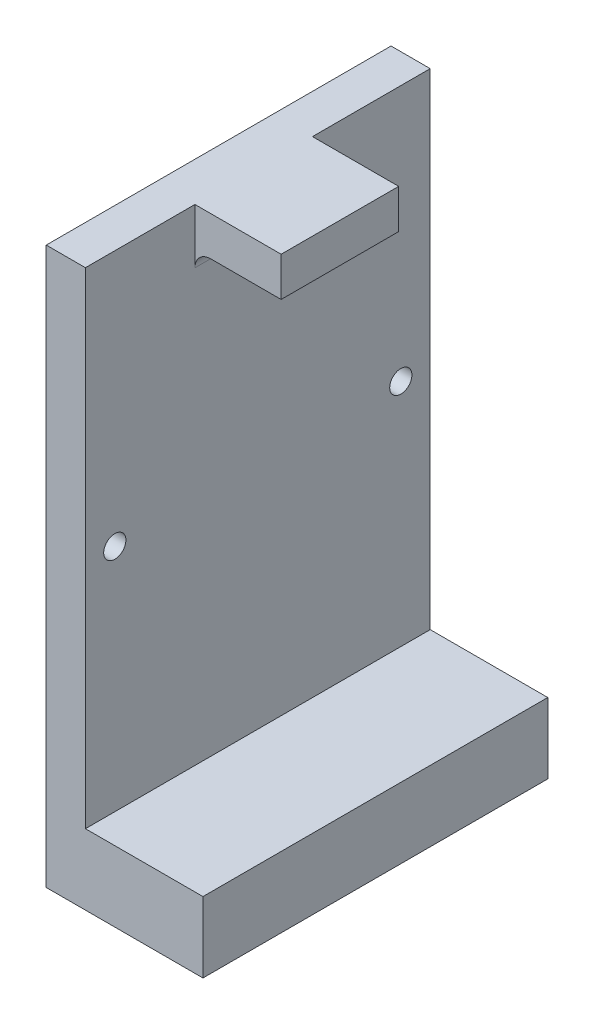
SolidWorks part; units mm, degrees
ref_plane "Front Plane" through (0, 0, 0) normal (0, 0, 1) x (1, 0, 0)
ref_plane "Top Plane" through (0, 0, 0) normal (0, 1, 0) x (1, 0, 0)
ref_plane "Right Plane" through (0, 0, 0) normal (1, 0, 0) x (0, 0, -1)
sketch "Sketch1" plane through (0, 0, 0) normal (0, 1, 0) x (1, 0, 0)
  line L1 (0, 0) -> (-25.4, 0)
  line L2 (0, 0) -> (0, 55.88)
  line L3 (0, 55.88) -> (-25.4, 55.88)
  line L4 (-25.4, 0) -> (-25.4, 55.88)
  dimension "D1" = 55.88
  dimension "D2" = 25.4
extrude "Boss-Extrude1" add sketch "Sketch1" along normal blind 11.43
sketch "Sketch3" plane through (0, 11.43, 0) normal (0, 1, 0) x (1, 0, 0)
  line L0 (-25.4, 0) -> (0, 0) construction
  line L1 (-25.4, 55.88) -> (-19.05, 55.88)
  line L2 (-25.4, 55.88) -> (-25.4, 0)
  line L3 (-25.4, 0) -> (-19.05, 0)
  line L4 (-19.05, 55.88) -> (-19.05, 0)
  dimension "D1" = 6.35
extrude "Boss-Extrude2" add sketch "Sketch3" along normal blind 78.74
sketch "Sketch4" plane through (-19.05, 0, 0) normal (1, 0, 0) x (0, 0, -1)
  line L0 (0, 90.17) -> (55.88, 90.17) construction
  line L1 (17.7495, 90.17) -> (36.7995, 90.17)
  line L2 (17.7495, 90.17) -> (17.7495, 83.82)
  line L3 (17.7495, 83.82) -> (36.7995, 83.82)
  line L4 (36.7995, 90.17) -> (36.7995, 83.82)
  dimension "D1" = 19.05
  dimension "D2" = 6.35
extrude "Boss-Extrude3" add sketch "Sketch4" along normal blind 13.97
hole_wizard "M3 Clearance Hole1" positions "Sketch5" profile "Sketch6" hole size "M3" standard "ANSI Metric" end condition through all
sketch "Sketch5" plane through (-19.05, 0, 0) normal (1, 0, 0) x (0, 0, -1)
  line L0 (0, 90.17) -> (0, 11.43) construction
  point P0 (4.7625, 48.6673)
  point P2 (51.1175, 48.6673)
  dimension "D1" = 46.355
  dimension "D2" = 4.7625
sketch "Sketch6" plane through (-19.05, 48.6673, -4.7625) normal (0, 1, 0) x (0, 0, -1)
  line L0 (0, 0) -> (0, 6.35)
  line L1 (0, 6.35) -> (1.8, 6.35)
  line L2 (1.8, 6.35) -> (1.8, 0)
  line L5 (1.8, 0) -> (0, 0)
  line L11 (0, -6.35) -> (0, 107.95) construction
  dimension "Thru Hole Dia." = 3.6
  dimension "Thru Hole Depth" = 6.35
fillet "Fillet1" radius 2.54 1 edges at (-19.05, 83.82, -27.2745)
ref_plane "Plane1" through (0, 0, -27.94) normal (0, 0, 1) x (1, 0, 0)
